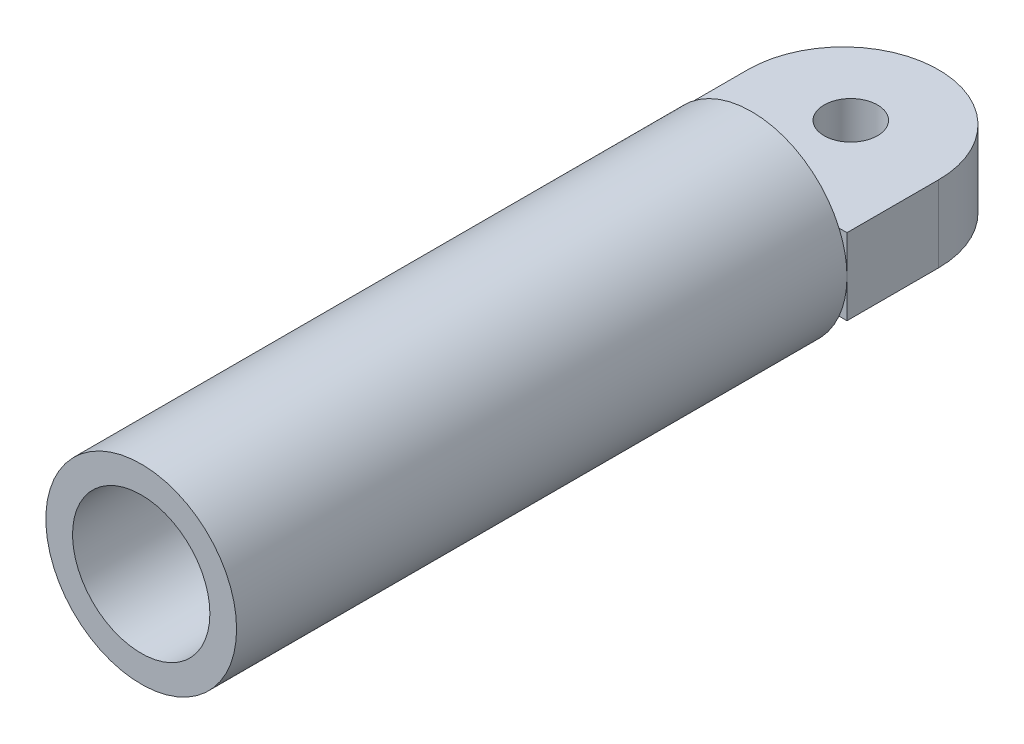
SolidWorks part; units mm, degrees
ref_plane "Front Plane" through (0, 0, 0) normal (0, 0, 1) x (1, 0, 0)
ref_plane "Top Plane" through (0, 0, 0) normal (0, 1, 0) x (1, 0, 0)
ref_plane "Right Plane" through (0, 0, 0) normal (1, 0, 0) x (0, 0, -1)
sketch "Sketch1" plane through (0, 0, 0) normal (0, 0, 1) x (1, 0, 0)
  circle A0 centre (0, 0) radius 12.5
  circle A1 centre (0, 0) radius 9
  dimension "D1" = 25
  dimension "D2" = 18
extrude "Boss-Extrude1" add sketch "Sketch1" along normal blind 80
sketch "Sketch2" plane through (0, 0, 0) normal (0, 1, 0) x (1, 0, 0)
  line L1 (-12.5, 0) -> (12.5, 0)
  line L2 (-12.5, 0) -> (-12.5, 12)
  line L4 (12.5, 0) -> (12.5, 12)
  arc A0 (-12.5, 12) -> (12.5, 12) centre (0, 12) cw
  circle A3 centre (0, 13) radius 3.5
  dimension "D1" = 12.5
  dimension "D3" = 7
  dimension "D2" = 12
  dimension "D4" = 13
extrude "Boss-Extrude2" add sketch "Sketch2" along normal mid plane 10
